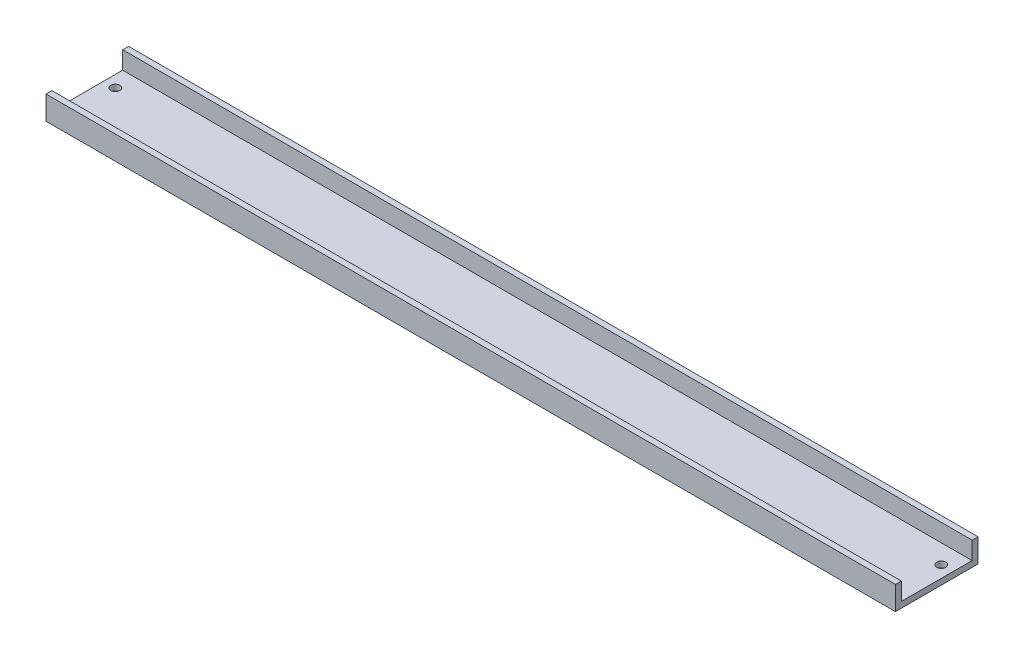
SolidWorks part; units mm, degrees
ref_plane "Front Plane" through (0, 0, 0) normal (0, 0, 1) x (1, 0, 0)
ref_plane "Top Plane" through (0, 0, 0) normal (0, 1, 0) x (1, 0, 0)
ref_plane "Right Plane" through (0, 0, 0) normal (1, 0, 0) x (0, 0, -1)
sketch "Sketch1" plane through (0, 0, 0) normal (1, 0, 0) x (0, 0, -1)
  line L1 (0, 0) -> (44.45, 0)
  line L2 (0, 0) -> (0, 12.7)
  line L3 (0, 12.7) -> (44.45, 12.7)
  line L4 (44.45, 0) -> (44.45, 12.7)
extrude "Boss-Extrude1" add sketch "Sketch1" along normal blind 457.2 contours L2 L1 L4 L3
sketch "Sketch2" plane through (0, 0, 0) normal (-1, 0, 0) x (0, 0, 1)
  line L0 (-41.275, 12.7) -> (-3.175, 12.7)
  line L1 (-41.275, 12.7) -> (-41.275, 3.175)
  line L2 (-41.275, 3.175) -> (-3.175, 3.175)
  line L3 (-3.175, 12.7) -> (-3.175, 3.175)
  line L4 (0, 12.7) -> (-44.45, 12.7) construction
  point P6 (0, 0)
  point P7 (0, 0)
  point P8 (0, 0)
  point P9 (0, 0)
extrude "Cut-Extrude1" cut sketch "Sketch2" against normal blind 457.2
hole_wizard "#10 (0.1935) Diameter Hole3" positions "3DSketch12" profile "Sketch14" hole size "#10" standard "ANSI Inch" end condition through all
sketch3d "3DSketch12"
  point P0 (450.8327, 0, -31.0166)
  point P2 (450.8147, 0, -5.6087)
  point P4 (6.29, 0, -31.0487)
  point P6 (6.23, 0, -5.6032)
sketch "Sketch14" plane through (450.8327, 0, -31.0166) normal (1, 0, 0) x (0, 0, -1)
  line L0 (0, 0) -> (0, 12.7)
  line L1 (0, 12.7) -> (2.4574, 12.7)
  line L2 (2.4574, 12.7) -> (2.4574, 0)
  line L5 (2.4574, 0) -> (0, 0)
  line L11 (0, -6.35) -> (0, 107.95) construction
  dimension "Thru Hole Dia." = 4.9149
  dimension "Thru Hole Depth" = 12.7
sketch "Sketch15" plane through (0, 0, 0) normal (0, -1, 0) x (1, 0, 0)
